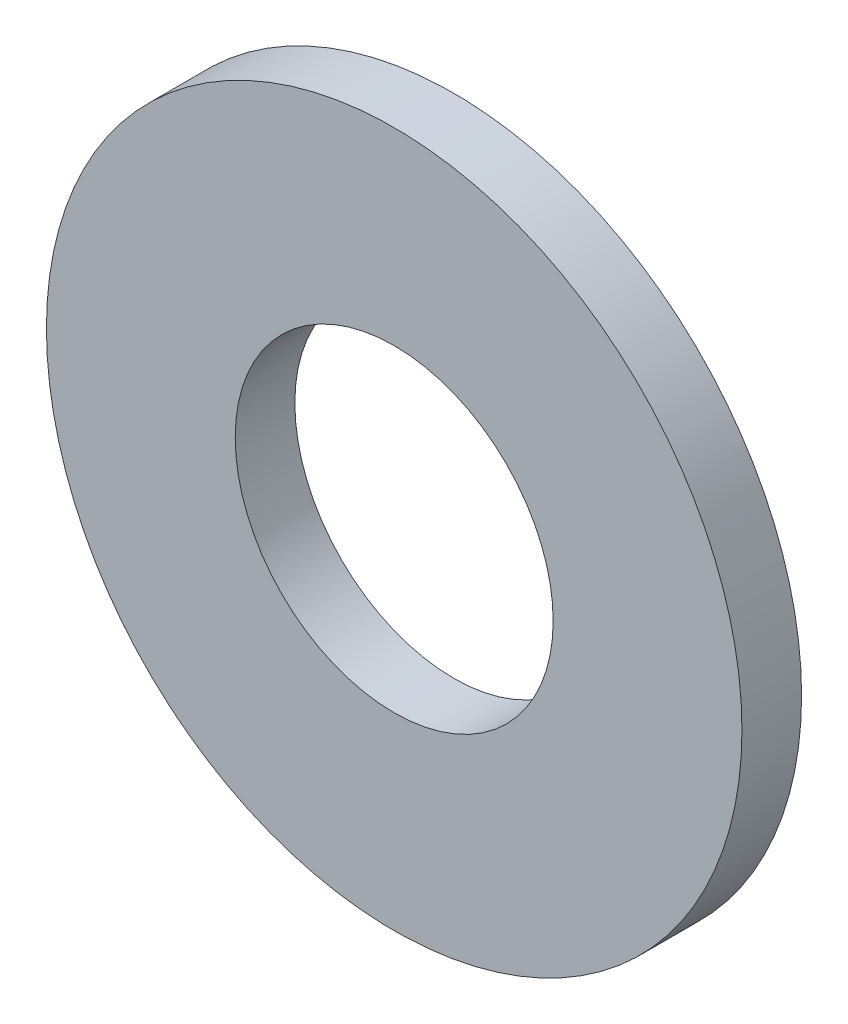
SolidWorks part; units mm, degrees
ref_plane "Front Plane" through (0, 0, 0) normal (0, 0, 1) x (1, 0, 0)
ref_plane "Top Plane" through (0, 0, 0) normal (0, 1, 0) x (1, 0, 0)
ref_plane "Right Plane" through (0, 0, 0) normal (1, 0, 0) x (0, 0, -1)
sketch "Sketch1" plane through (0, 0, 0) normal (0, 0, 1) x (1, 0, 0)
  circle A0 centre (0, 0) radius 3.5
  circle A1 centre (0, 0) radius 1.6
  dimension "OD" = 7
  dimension "ID1" = 3.2
extrude "Boss-Extrude1" add sketch "Sketch1" along normal blind 0.6
